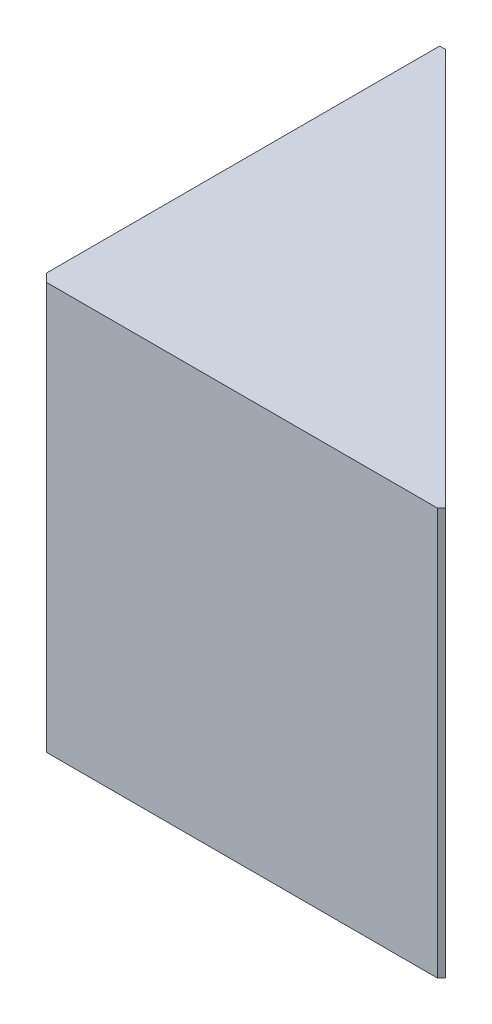
SolidWorks part; units mm, degrees
material "玻璃"
ref_plane "前视基准面" through (0, 0, 0) normal (0, 0, 1) x (1, 0, 0)
ref_plane "上视基准面" through (0, 0, 0) normal (0, 1, 0) x (1, 0, 0)
ref_plane "右视基准面" through (0, 0, 0) normal (1, 0, 0) x (0, 0, -1)
sketch "草图1" plane through (0, 0, 0) normal (0, 1, 0) x (1, 0, 0)
  line L1 (-2.5, 2.5) -> (2.5, 2.5)
  line L2 (-2.5, 2.5) -> (-2.5, -2.5)
  line L3 (-2.5, -2.5) -> (2.5, -2.5)
  line L4 (2.5, 2.5) -> (2.5, -2.5)
  line L5 (-2.5, 2.5) -> (2.5, -2.5) construction
  line L6 (-2.5, -2.5) -> (2.5, 2.5) construction
  point P0 (0, 0)
  dimension "D1" = 5
  dimension "D2" = 5
extrude "凸台-拉伸1" add sketch "草图1" along normal blind 5
sketch "草图2" plane through (0, 5, 0) normal (0, 1, 0) x (1, 0, 0)
  line L0 (-2.5, 2.5) -> (2.5, -2.5)
  line L1 (2.5, -2.5) -> (2.5, 2.5)
  line L2 (2.5, 2.5) -> (-2.5, 2.5)
extrude "切除-拉伸1" cut sketch "草图2" against normal blind 5
chamfer "倒角1" distance 0.1 angle 45 3 edges at (-2.5, 2.5, -2.5) (2.5, 2.5, 2.5) (-2.5, 2.5, 2.5)
